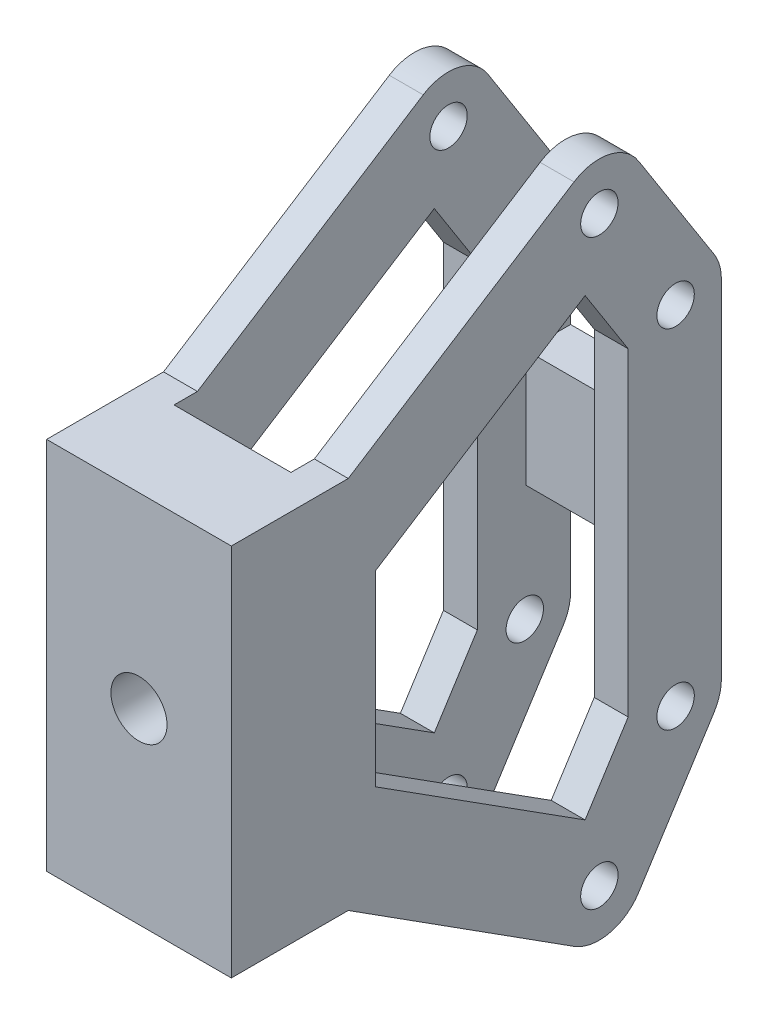
SolidWorks part; units mm, degrees
ref_plane "Front Plane" through (0, 0, 0) normal (0, 0, 1) x (1, 0, 0)
ref_plane "Top Plane" through (0, 0, 0) normal (0, 1, 0) x (1, 0, 0)
ref_plane "Right Plane" through (0, 0, 0) normal (1, 0, 0) x (0, 0, -1)
sketch "Sketch1" plane through (0, 0, 0) normal (1, 0, 0) x (0, 0, -1)
  line L0 (0, -40) -> (0, 40)
  line L1 (0, 40) -> (25, 40)
  line L2 (25, 40) -> (73.2801, 70.7854)
  line L3 (87.0883, 67.7301) -> (103.2229, 42.4264)
  line L4 (104.7912, 37.05) -> (104.7912, -37.05)
  line L5 (-32.2378, 0) -> (212.0044, 0) construction
  line L6 (30.81, -20) -> (30.81, 20)
  line L7 (30.81, 20) -> (75.6511, 48.5528)
  line L8 (75.6511, 48.5528) -> (84.8572, 34.095)
  line L9 (84.8572, 34.095) -> (84.8572, -34.095)
  line L10 (75.6511, -48.5528) -> (84.8572, -34.095)
  line L11 (30.81, -20) -> (75.6511, -48.5528)
  line L12 (87.0883, -67.7301) -> (103.2229, -42.4264)
  line L13 (25, -40) -> (73.2801, -70.7854)
  line L14 (0, -40) -> (25, -40)
  arc A0 (73.2801, 70.7854) -> (87.0883, 67.7301) centre (78.6565, 62.3536) cw
  arc A1 (103.2229, 42.4264) -> (104.7912, 37.05) centre (94.7912, 37.05) cw
  circle A3 centre (78.7, 62.25) radius 4
  circle A4 centre (95, 37.1536) radius 4
  circle A5 centre (95, -37.1536) radius 4
  circle A6 centre (78.7, -62.25) radius 4
  arc A7 (103.2229, -42.4264) -> (104.7912, -37.05) centre (94.7912, -37.05) ccw
  arc A8 (73.2801, -70.7854) -> (87.0883, -67.7301) centre (78.6565, -62.3536) ccw
  point P15 (0, 0)
  point P24 (84.8572, 0)
  point P25 (30.81, 0)
  point P26 (104.7912, 0)
  point P27 (0, 0)
  dimension "D4" = 10
  dimension "D6" = 10
  dimension "D15" = 8
  dimension "D18" = 8
  dimension "D1" = 40
  dimension "D2" = 25
  dimension "D3" = 57.26
  dimension "D5" = 30.01
  dimension "D7" = 37.05
  dimension "D8" = 30.81
  dimension "D9" = 20
  dimension "D10" = 53.16
  dimension "D11" = 17.14
  dimension "D12" = 34.095
  dimension "D13" = 22.25
  dimension "D14" = 78.7
  dimension "D16" = 25.2
  dimension "D17" = 95
extrude "Boss-Extrude1" add sketch "Sketch1" along normal blind 39.5
sketch "Sketch2" plane through (0, 0, 0) normal (0, 1, 0) x (1, 0, 0)
  line L0 (19.75, 0) -> (19.75, 126.714) construction
  line L1 (39.5, 0) -> (0, 0) construction
  line L3 (7.25, 95.25) -> (32.25, 95.25)
  line L4 (7.25, 95.25) -> (7.25, 20)
  line L5 (7.25, 20) -> (32.25, 20)
  line L6 (32.25, 95.25) -> (32.25, 20)
  line L7 (7.25, 95.25) -> (32.25, 20) construction
  line L8 (7.25, 20) -> (32.25, 95.25) construction
  point P4 (19.75, 57.625)
  dimension "D1" = 75.25
  dimension "D2" = 25
  dimension "D3" = 20
extrude "Cut-Extrude1" cut sketch "Sketch2" against normal blind 117.5 and the other way blind 105.5
sketch "Sketch3" plane through (0, 0, -104.7912) normal (0, 0, -1) x (-1, 0, 0)
  line L2 (-39.5, -37.05) -> (0, -37.05) construction
  line L3 (-7.25, -37.05) -> (-7.25, -12.5)
  line L4 (-7.25, -12.5) -> (-32.25, -12.5)
  line L5 (-32.25, -12.5) -> (-32.25, -37.05)
  line L9 (-39.5, 37.05) -> (0, 37.05) construction
  line L10 (-32.25, 37.05) -> (-32.25, 12.5)
  line L11 (-32.25, 12.5) -> (-7.25, 12.5)
  line L12 (-7.25, 12.5) -> (-7.25, 37.05)
  line L16 (-32.25, 54.9301) -> (-32.25, 37.05)
  line L17 (-7.25, 54.9301) -> (-7.25, 37.05)
  line L18 (-32.25, 54.9301) -> (-7.25, 54.9301)
  line L19 (-32.25, -37.05) -> (-32.25, -54.9301)
  line L20 (-32.25, -54.9301) -> (-7.25, -54.9301)
  line L21 (-7.25, -54.9301) -> (-7.25, -37.05)
  dimension "D5" = 24.55
  dimension "D6" = 24.55
extrude "Cut-Extrude2" cut sketch "Sketch3" against normal blind 43.5
sketch "Sketch4" plane through (0, 0, 0) normal (0, 0, 1) x (1, 0, 0)
  line L1 (19.75, 40) -> (19.75, 55.4414) construction
  line L2 (39.5, 40) -> (0, 40) construction
  line L3 (0, 0) -> (19.75, 0) construction
  line L4 (0, 40) -> (0, -40) construction
  line L5 (19.75, 40) -> (19.75, 0) construction
  circle A1 centre (19.75, 0) radius 6
  dimension "D1" = 12
extrude "Cut-Extrude3" cut sketch "Sketch4" against normal blind 41
